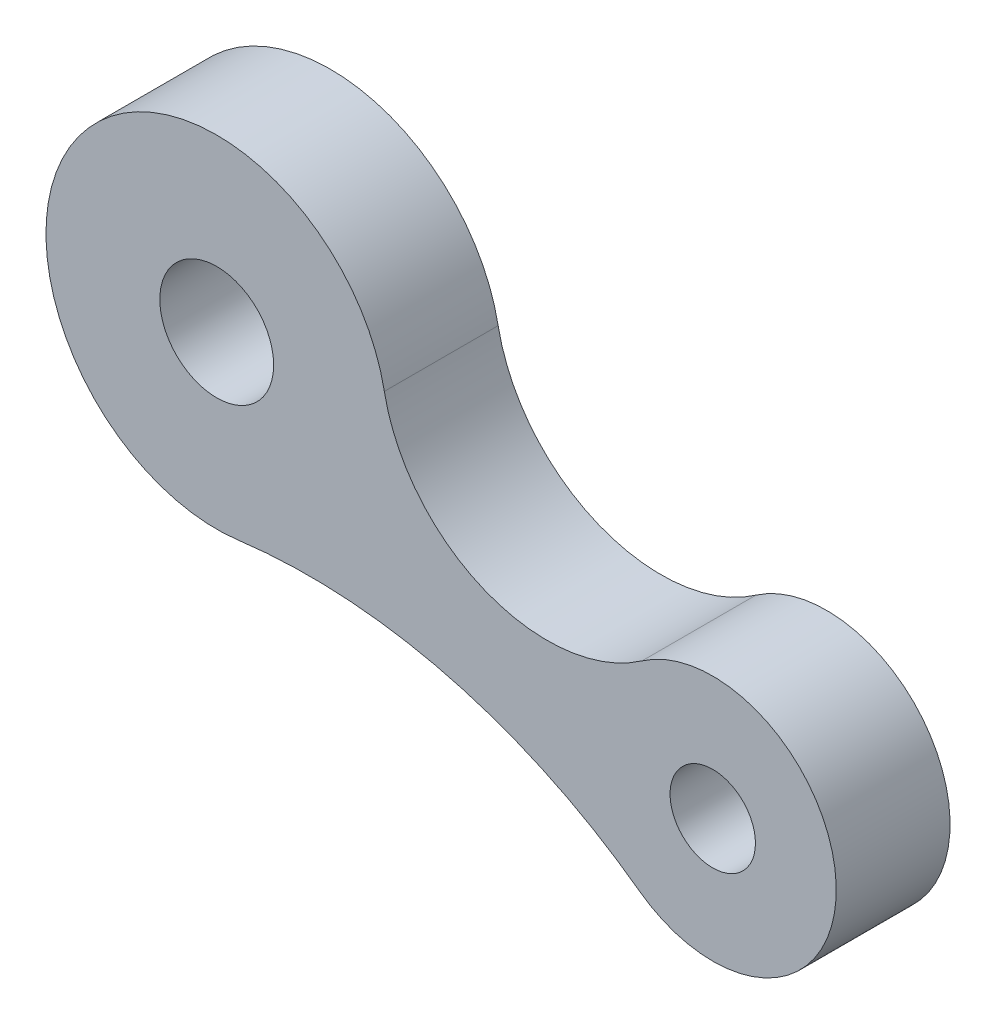
SolidWorks part; units mm, degrees
ref_plane "前视基准面" through (0, 0, 0) normal (0, 0, 1) x (1, 0, 0)
ref_plane "上视基准面" through (0, 0, 0) normal (0, 1, 0) x (1, 0, 0)
ref_plane "右视基准面" through (0, 0, 0) normal (1, 0, 0) x (0, 0, -1)
sketch "草图1" plane through (0, 0, 0) normal (0, 0, 1) x (1, 0, 0)
  line L0 (0, 0) -> (591.7989, 0) construction
  arc A0 (27.4298, 11.4225) -> (-23.8332, -59.5116) centre (-31.4729, 0) ccw
  arc A1 (117.172, -95.8964) -> (118.0116, -25.2992) centre (142.8367, -60.898) ccw
  arc A2 (27.4298, 11.4225) -> (118.0116, -25.2992) centre (84.6636, 22.5213) ccw
  arc A3 (117.172, -95.8964) -> (-23.8332, -59.5116) centre (1.1487, -254.1147) ccw
  circle A4 centre (-31.4729, 0) radius 20
  circle A5 centre (142.8367, -60.898) radius 15
  dimension "D1" = 60
  dimension "D2" = 58.3
  dimension "D3" = 43.4
  dimension "D4" = 196.2
  dimension "D5" = 30
  dimension "D6" = 40
extrude "凸台-拉伸1" add sketch "草图1" along normal blind 40
